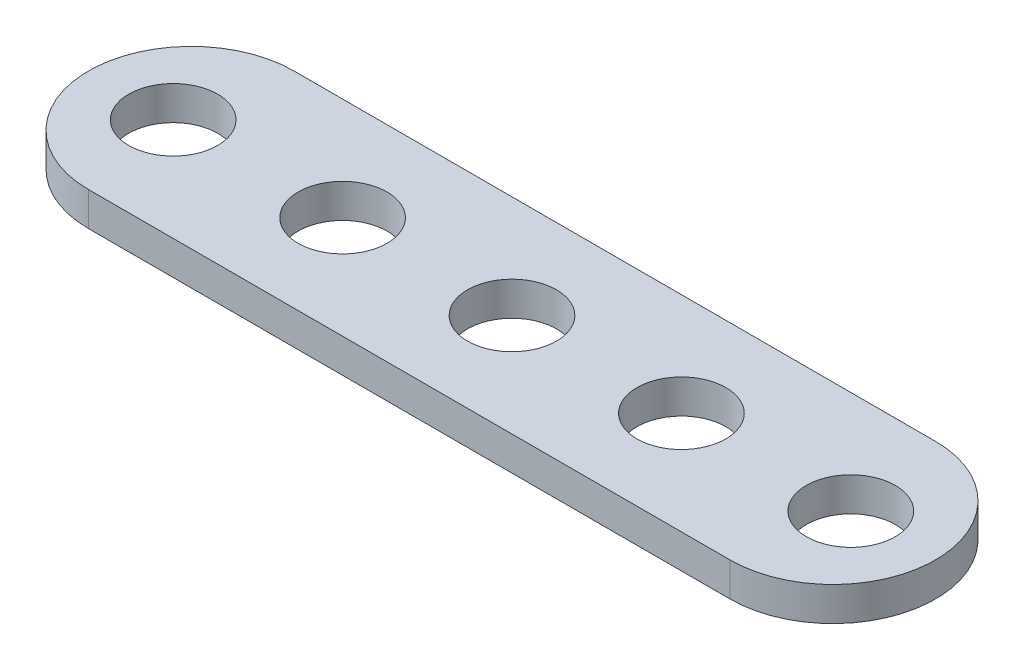
SolidWorks part; units mm, degrees
material "PA Type 6"
ref_plane "Front Plane" through (0, 0, 0) normal (0, 0, 1) x (1, 0, 0)
ref_plane "Top Plane" through (0, 0, 0) normal (0, 1, 0) x (1, 0, 0)
ref_plane "Right Plane" through (0, 0, 0) normal (1, 0, 0) x (0, 0, -1)
sketch "Sketch1" plane through (0, 0, 0) normal (0, 1, 0) x (1, 0, 0)
  line L0 (4.85, 0) -> (35.15, 0) construction
  line L1 (4.85, 4.85) -> (35.15, 4.85)
  line L2 (4.85, -4.85) -> (35.15, -4.85)
  arc A0 (4.85, 4.85) -> (4.85, -4.85) centre (4.85, 0) ccw
  arc A1 (35.15, -4.85) -> (35.15, 4.85) centre (35.15, 0) ccw
  point P3 (20, 0)
  dimension "D2" = 40
  dimension "D1" = 9.7
extrude "Boss-Extrude1" add sketch "Sketch1" along normal blind 1.6
sketch "Sketch2" plane through (0, 1.6, 0) normal (0, 1, 0) x (1, 0, 0)
  line L0 (-3.846, 0) -> (27.4208, 0) construction
  line L1 (4.85, -4.85) -> (35.15, -4.85) construction
  circle A0 centre (4, 0) radius 2.1
  arc A1 (4.85, 4.85) -> (4.85, -4.85) centre (4.85, 0) ccw construction
  point P2 (0, 0)
  dimension "D2" = 4.2
  dimension "D1" = 4
extrude "Cut-Extrude1" cut sketch "Sketch2" against normal through all
pattern_linear "LPattern1" count 5 spacing 8 along (1, 0, 0) of "Cut-Extrude1"
